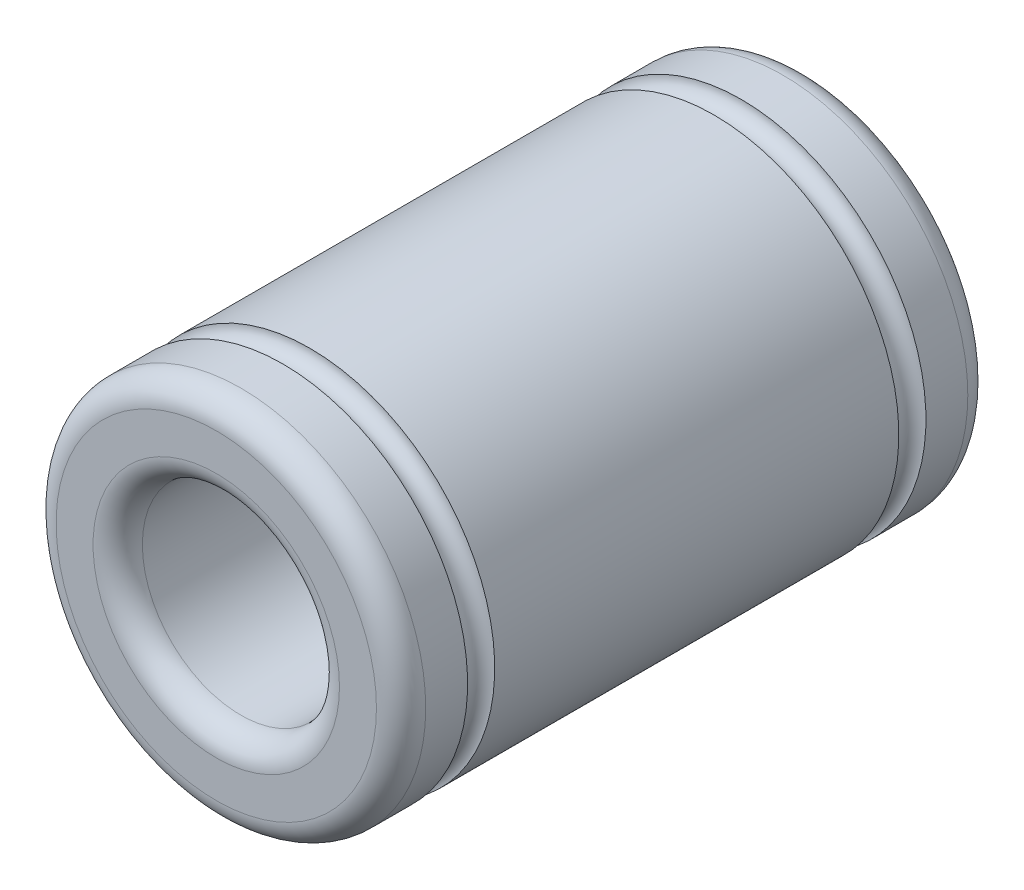
SolidWorks part; units mm, degrees
ref_plane "Front Plane" through (0, 0, 0) normal (0, 0, 1) x (1, 0, 0)
ref_plane "Top Plane" through (0, 0, 0) normal (0, 1, 0) x (1, 0, 0)
ref_plane "Right Plane" through (0, 0, 0) normal (1, 0, 0) x (0, 0, -1)
sketch "Sketch1" plane through (0, 0, 0) normal (0, 0, 1) x (1, 0, 0)
  circle A0 centre (0, 0) radius 4
  circle A1 centre (0, 0) radius 7.5
  dimension "D1" = 8
  dimension "D2" = 15
extrude "Boss-Extrude1" add sketch "Sketch1" along normal blind 24
fillet "Fillet1" radius 1 4 edges at (7.5, 0, 0) (7.5, 0, 24) (4, 0, 0) (4, 0, 24)
sketch "Sketch2" plane through (0, 0, 0) normal (1, 0, 0) x (0, 0, -1)
  line L0 (-1, 7.5) -> (-23, 7.5) construction
  line L1 (-24, 6.5) -> (-24, -6.5) construction
  line L2 (-12, 7.5) -> (-12, 2.3498) construction
  line L3 (-24, 0) -> (0, 0) construction
  circle A0 centre (-20.75, 7.5) radius 0.55
  circle A2 centre (-3.25, 7.5) radius 0.55
  dimension "D1" = 1.1
  dimension "D2" = 3.25
revolve "Cut-Revolve1" cut sketch "Sketch2" angle 360 about L3
